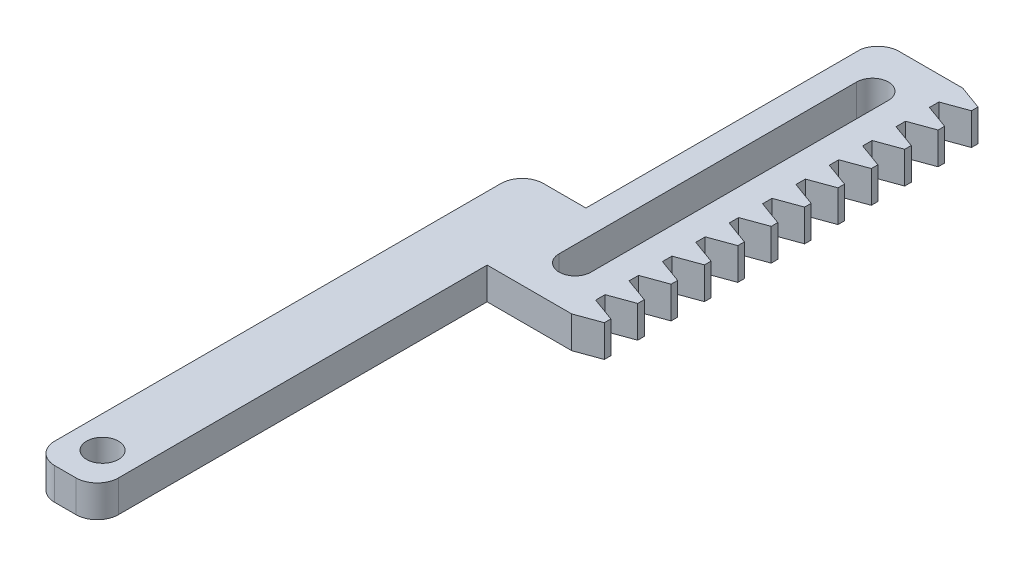
SolidWorks part; units mm, degrees
ref_plane "Alzado" through (0, 0, 0) normal (0, 0, 1) x (1, 0, 0)
ref_plane "Planta" through (0, 0, 0) normal (0, 1, 0) x (1, 0, 0)
ref_plane "Vista lateral" through (0, 0, 0) normal (1, 0, 0) x (0, 0, -1)
sketch "Croquis1" plane through (0, 0, 0) normal (0, 1, 0) x (1, 0, 0)
  line L8 (2.223, 8.5976) -> (-13.3901, 8.5976) construction
  line L62 (0.223, 27.0976) -> (6.223, 27.0976)
  line L63 (2.223, 22.5976) -> (2.223, -5.4024) construction
  line L66 (3.723, 22.5976) -> (3.723, -5.4024)
  line L67 (2.223, 22.5976) -> (2.223, 27.0976) construction
  line L68 (0.723, 22.5976) -> (0.723, -5.4024)
  line L69 (7.473, 30.861) -> (7.473, -7.9403) construction
  line L70 (6.223, -9.7127) -> (0.2568, -9.7127)
  line L72 (-1.7432, 25.4637) -> (-1.7432, -0.4127)
  line L74 (-1.7432, -0.4127) -> (-5.7432, -0.4127)
  line L75 (-7.7432, -2.4127) -> (-7.7432, -4.4127)
  line L76 (-5.7432, -6.4127) -> (-1.7432, -6.4127) construction
  line L77 (-1.7432, -6.4127) -> (-1.7432, -7.7127) construction
  line L78 (-7.7432, -4.4127) -> (-7.7432, -6.4127)
  line L79 (-7.7432, -6.4127) -> (-5.7432, -6.4127) construction
  line L80 (-7.7432, -6.4127) -> (-7.7432, -44.4127)
  line L81 (-1.7432, -9.7127) -> (-1.7432, -44.4127)
  line L82 (-3.7432, -46.4127) -> (-5.7432, -46.4127)
  line L84 (-1.7432, -9.7127) -> (0.2568, -9.7127)
  arc A13 (-1.7432, 25.4637) -> (0.223, 27.0976) centre (0.223, 25.0976) cw
  arc A20 (3.723, 22.5976) -> (0.723, 22.5976) centre (2.223, 22.5976) ccw
  arc A21 (0.723, -5.4024) -> (3.723, -5.4024) centre (2.223, -5.4024) ccw
  arc A22 (0.2568, -9.7127) -> (-1.7432, -7.7127) centre (0.2568, -7.7127) cw construction
  circle A23 centre (-4.7432, -3.4127) radius 1.5 construction
  arc A24 (-5.7432, -6.4127) -> (-7.7432, -4.4127) centre (-5.7432, -4.4127) cw construction
  arc A25 (-7.7432, -2.4127) -> (-5.7432, -0.4127) centre (-5.7432, -2.4127) cw
  arc A26 (-5.7432, -46.4127) -> (-7.7432, -44.4127) centre (-5.7432, -44.4127) cw
  arc A27 (-1.7432, -44.4127) -> (-3.7432, -46.4127) centre (-3.7432, -44.4127) cw
  circle A28 centre (-4.7432, -42.9127) radius 1.5
  point P5 (2.223, 8.5976)
  point P36 (-7.7432, -46.4127)
  line B0 (6.223, 24.8449) -> (6.223, 23.956)
  line B1 (6.223, 24.8449) -> (8.473, 25.6638)
  line B2 (8.473, 25.6638) -> (8.473, 26.2786)
  line B3 (6.223, 27.0976) -> (8.473, 26.2786)
  line B4 (6.223, 21.7033) -> (6.223, 20.8144)
  line B5 (6.223, 21.7033) -> (8.473, 22.5222)
  line B6 (8.473, 22.5222) -> (8.473, 23.1371)
  line B7 (6.223, 23.956) -> (8.473, 23.1371)
  line B8 (6.223, 18.5617) -> (6.223, 17.6728)
  line B9 (6.223, 18.5617) -> (8.473, 19.3806)
  line B10 (8.473, 19.3806) -> (8.473, 19.9955)
  line B11 (6.223, 20.8144) -> (8.473, 19.9955)
  line B12 (6.223, 12.2785) -> (6.223, 11.3896)
  line B13 (6.223, 12.2785) -> (8.473, 13.0974)
  line B14 (8.473, 13.0974) -> (8.473, 13.7123)
  line B15 (6.223, 14.5312) -> (8.473, 13.7123)
  line B16 (6.223, 15.4201) -> (6.223, 14.5312)
  line B17 (6.223, 15.4201) -> (8.473, 16.239)
  line B18 (8.473, 16.239) -> (8.473, 16.8539)
  line B19 (6.223, 17.6728) -> (8.473, 16.8539)
  line B20 (6.223, 9.1369) -> (6.223, 8.248)
  line B21 (6.223, 9.1369) -> (8.473, 9.9558)
  line B22 (8.473, 9.9558) -> (8.473, 10.5707)
  line B23 (6.223, 11.3896) -> (8.473, 10.5707)
  line B24 (6.223, 2.8537) -> (6.223, 1.9648)
  line B25 (6.223, 2.8537) -> (8.473, 3.6726)
  line B26 (8.473, 3.6726) -> (8.473, 4.2875)
  line B27 (6.223, 5.1064) -> (8.473, 4.2875)
  line B28 (6.223, 5.9953) -> (6.223, 5.1064)
  line B29 (6.223, 5.9953) -> (8.473, 6.8142)
  line B30 (8.473, 6.8142) -> (8.473, 7.4291)
  line B31 (6.223, 8.248) -> (8.473, 7.4291)
  line B32 (6.223, -0.2879) -> (6.223, -1.1768)
  line B33 (6.223, -0.2879) -> (8.473, 0.531)
  line B34 (8.473, 0.531) -> (8.473, 1.1459)
  line B35 (6.223, 1.9648) -> (8.473, 1.1459)
  line B36 (6.223, -3.4295) -> (6.223, -4.3183)
  line B37 (6.223, -3.4295) -> (8.473, -2.6105)
  line B38 (8.473, -2.6105) -> (8.473, -1.9957)
  line B39 (6.223, -1.1768) -> (8.473, -1.9957)
  line B40 (6.223, -9.7127) -> (8.473, -8.8937)
  line B41 (8.473, -8.8937) -> (8.473, -8.2789)
  line B42 (6.223, -7.4599) -> (8.473, -8.2789)
  line B43 (6.223, -6.5711) -> (6.223, -7.4599)
  line B44 (6.223, -6.5711) -> (8.473, -5.7521)
  line B45 (8.473, -5.7521) -> (8.473, -5.1373)
  line B46 (6.223, -4.3183) -> (8.473, -5.1373)
  dimension "D5" = 1.5
  dimension "D6" = 4
  dimension "D7" = 4.5
  dimension "D9" = 6.3
  dimension "D12" = 3
  dimension "D8" = 28
  dimension "D13" = 90
  dimension "D15" = 3
  dimension "D16" = 2
  dimension "D17" = 40
  dimension "D3" = 2
  dimension "D4" = 2
  dimension "D10" = 3
  dimension "D11" = 3
  dimension "D14" = 3
  dimension "D18" = 2
  dimension "D19" = 2
  dimension "D20" = 3
  dimension "D1" = 1
  dimension "D2" = 6
  dimension "D21" = 3.5
sketch_block_instance "Bloque1-65"
sketch_block "Bloque1"
sketch_block_instance "Bloque1-66"
sketch_block_instance "Bloque1-67"
sketch_block_instance "Bloque1-68"
sketch_block_instance "Bloque1-69"
sketch_block_instance "Bloque1-70"
sketch_block_instance "Bloque1-71"
sketch_block_instance "Bloque1-72"
sketch_block_instance "Bloque1-73"
sketch_block_instance "Bloque1-74"
sketch_block_instance "Bloque2-4"
sketch_block "Bloque2"
sketch_block_instance "Bloque1-75"
extrude "Saliente-Extruir2" add sketch "Croquis1" along normal blind 3
